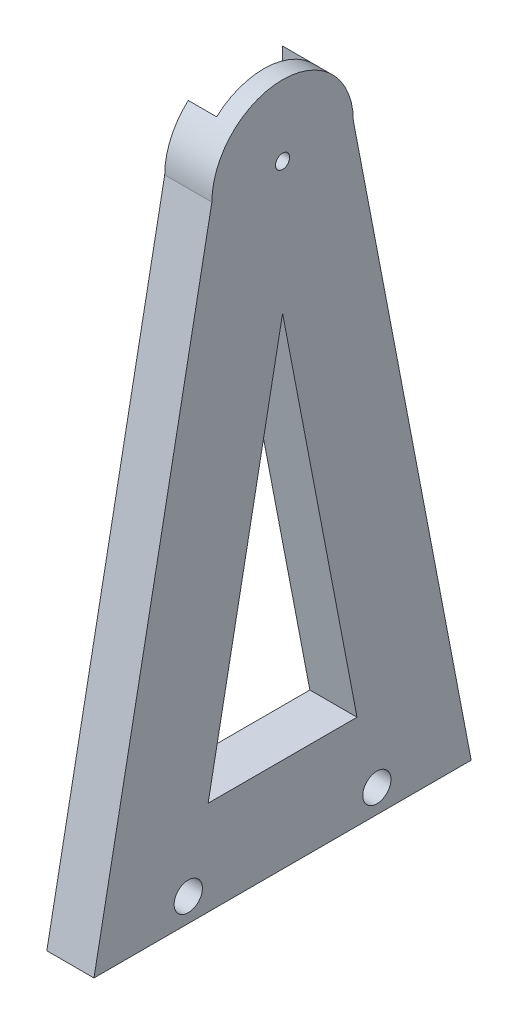
SolidWorks part; units mm, degrees
ref_plane "Front Plane" through (0, 0, 0) normal (0, 0, 1) x (1, 0, 0)
ref_plane "Top Plane" through (0, 0, 0) normal (0, 1, 0) x (1, 0, 0)
ref_plane "Right Plane" through (0, 0, 0) normal (1, 0, 0) x (0, 0, -1)
sketch "Sketch2" plane through (0, 0, 0) normal (1, 0, 0) x (0, 0, -1)
  line L0 (0, 0) -> (0, 130) construction
  line L1 (40, 0) -> (-40, 0)
  line L2 (-40, 0) -> (-15, 130)
  line L3 (40, 0) -> (15, 130)
  circle A0 centre (0, 130) radius 10 construction
  arc A1 (15, 130) -> (-15, 130) centre (0, 130) ccw
  dimension "D2" = 20
  dimension "D3" = 30
  dimension "D1" = 130
  dimension "D4" = 40
extrude "Boss-Extrude1" add sketch "Sketch2" along normal blind 10
sketch "Sketch3" plane through (0, 0, 0) normal (-1, 0, 0) x (0, 0, 1)
  line L0 (-10, 130) -> (-10, 151.1265)
  line L1 (-10, 151.1265) -> (10, 151.1265)
  line L2 (10, 151.1265) -> (10, 130)
  arc A0 (-10, 130) -> (10, 130) centre (0, 130) ccw
  dimension "D1" = 20
extrude "Cut-Extrude1" cut sketch "Sketch3" against normal blind 6
sketch "Sketch4" plane through (0, 0, 0) normal (-1, 0, 0) x (0, 0, 1)
  line L0 (40, 0) -> (-40, 0) construction
  line L1 (0, 0) -> (0, 16.8216) construction
  circle A0 centre (20, 5) radius 1.65
  circle A1 centre (-20, 5) radius 1.65
  dimension "D1" = 5
  dimension "D2" = 3.3
  dimension "D3" = 20
extrude "Cut-Extrude2" cut sketch "Sketch4" against normal through all
sketch "Sketch5" plane through (10, 0, 0) normal (1, 0, 0) x (0, 0, -1)
  circle A0 centre (-20, 5) radius 3
  circle A1 centre (20, 5) radius 3
  dimension "D1" = 6
  dimension "D2" = 6
extrude "Cut-Extrude3" cut sketch "Sketch5" against normal blind 5
sketch "Sketch6" plane through (6, 0, 0) normal (-1, 0, 0) x (0, 0, 1)
  circle A0 centre (0, 130) radius 1.5
  dimension "D1" = 3
extrude "Cut-Extrude4" cut sketch "Sketch6" against normal through all
sketch "Sketch7" plane through (0, 0, 0) normal (-1, 0, 0) x (0, 0, 1)
  line L0 (-15, 130) -> (-40, 0) construction
  line L1 (-40, 0) -> (40, 0) construction
  line L2 (40, 0) -> (15, 130) construction
  line L3 (15, 130) -> (-15, 130) construction
  line L4 (0, 102.0944) -> (-15.7874, 20)
  line L5 (-15.7874, 20) -> (15.7874, 20)
  line L6 (15.7874, 20) -> (0, 102.0944)
  line L7 (0, 102.0944) -> (0, 102.0944)
  dimension "D1" = 20
extrude "Cut-Extrude6" cut sketch "Sketch7" against normal through all contours L4 L5 L6 L7
